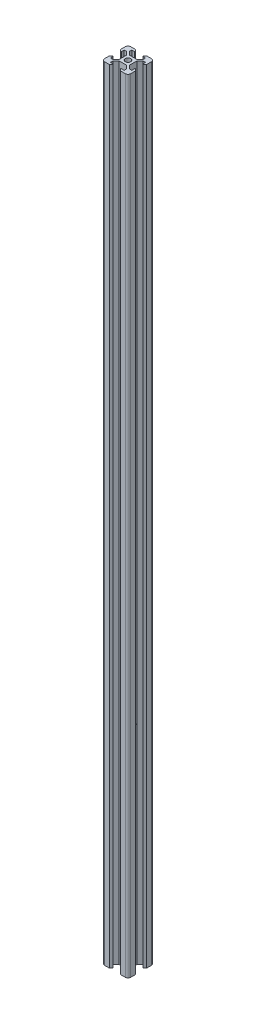
SolidWorks part; units mm, degrees
material "6063-T6"
ref_plane "Alzado" through (0, 0, 0) normal (0, 0, 1) x (1, 0, 0)
ref_plane "Planta" through (0, 0, 0) normal (0, 1, 0) x (1, 0, 0)
ref_plane "Vista lateral" through (0, 0, 0) normal (1, 0, 0) x (0, 0, -1)
sketch "Croquis1" plane through (0, 0, 0) normal (0, 1, 0) x (1, 0, 0)
  line L0 (0, 0) -> (-10, 10) construction
  line L1 (3.9, -2.84) -> (3.9, 2.84)
  line L2 (8.2, 5.3) -> (8.2, 3.34)
  line L3 (10, 8) -> (10, 4.14)
  line L4 (8.2, 5.3) -> (6.36, 5.3)
  line L5 (3.9, 2.84) -> (6.36, 5.3)
  line L6 (8.7, 2.84) -> (10, 4.14)
  line L7 (0, 0) -> (10, 10) construction
  line L8 (8, 10) -> (4.14, 10)
  line L9 (2.84, 8.7) -> (4.14, 10)
  line L10 (5.3, 8.2) -> (3.34, 8.2)
  line L11 (5.3, 8.2) -> (5.3, 6.36)
  line L12 (2.84, 3.9) -> (5.3, 6.36)
  line L13 (-2.84, 3.9) -> (2.84, 3.9)
  line L14 (-2.84, -3.9) -> (-5.3, -6.36)
  line L15 (-30.7915, 0) -> (30.7915, 0) construction
  line L16 (3.9, -2.84) -> (6.36, -5.3)
  line L17 (8.2, -5.3) -> (6.36, -5.3)
  line L18 (8.2, -5.3) -> (8.2, -3.34)
  line L19 (8.7, -2.84) -> (10, -4.14)
  line L20 (10, -8) -> (10, -4.14)
  line L21 (8, -10) -> (4.14, -10)
  line L22 (2.84, -8.7) -> (4.14, -10)
  line L23 (5.3, -8.2) -> (3.34, -8.2)
  line L24 (5.3, -8.2) -> (5.3, -6.36)
  line L25 (2.84, -3.9) -> (5.3, -6.36)
  line L26 (-2.84, -3.9) -> (2.84, -3.9)
  line L27 (0, 0) -> (0, 15.4885) construction
  line L28 (0, 0) -> (0, -17.6665) construction
  line L29 (0, 0) -> (-18.0561, 0) construction
  line L30 (-5.3, -8.2) -> (-5.3, -6.36)
  line L31 (-5.3, -8.2) -> (-3.34, -8.2)
  line L32 (-2.84, -8.7) -> (-4.14, -10)
  line L33 (-8, -10) -> (-4.14, -10)
  line L34 (-10, -8) -> (-10, -4.14)
  line L35 (-8.7, -2.84) -> (-10, -4.14)
  line L36 (-8.2, -5.3) -> (-8.2, -3.34)
  line L37 (-8.2, -5.3) -> (-6.36, -5.3)
  line L38 (-3.9, -2.84) -> (-6.36, -5.3)
  line L39 (-2.84, 3.9) -> (-5.3, 6.36)
  line L40 (-5.3, 8.2) -> (-5.3, 6.36)
  line L41 (-5.3, 8.2) -> (-3.34, 8.2)
  line L42 (-2.84, 8.7) -> (-4.14, 10)
  line L43 (-8, 10) -> (-4.14, 10)
  line L44 (-8.7, 2.84) -> (-10, 4.14)
  line L45 (-3.9, 2.84) -> (-6.36, 5.3)
  line L46 (-8.2, 5.3) -> (-6.36, 5.3)
  line L47 (-10, 8) -> (-10, 4.14)
  line L48 (-8.2, 5.3) -> (-8.2, 3.34)
  line L49 (-3.9, -2.84) -> (-3.9, 2.84)
  arc A0 (8.2, 3.34) -> (8.7, 2.84) centre (8.7, 3.34) ccw
  arc A1 (3.34, 8.2) -> (2.84, 8.7) centre (3.34, 8.7) cw
  arc A2 (10, 8) -> (8, 10) centre (8, 8) ccw
  arc A3 (8.2, -3.34) -> (8.7, -2.84) centre (8.7, -3.34) cw
  arc A4 (10, -8) -> (8, -10) centre (8, -8) cw
  arc A5 (3.34, -8.2) -> (2.84, -8.7) centre (3.34, -8.7) ccw
  arc A6 (-3.34, -8.2) -> (-2.84, -8.7) centre (-3.34, -8.7) cw
  arc A7 (-10, -8) -> (-8, -10) centre (-8, -8) ccw
  arc A8 (-8.2, -3.34) -> (-8.7, -2.84) centre (-8.7, -3.34) ccw
  arc A9 (-10, 8) -> (-8, 10) centre (-8, 8) cw
  arc A10 (-3.34, 8.2) -> (-2.84, 8.7) centre (-3.34, 8.7) ccw
  arc A11 (-8.2, 3.34) -> (-8.7, 2.84) centre (-8.7, 3.34) cw
  circle A12 centre (0, 0) radius 2.1
  point P11 (8.2, 2.84)
  point P65 (0, -3.9)
  point P73 (0, 3.9)
  point P80 (-8.2, 2.84)
  dimension "D9" = 0.5
  dimension "D12" = 2
  dimension "D13" = 4.2
  dimension "D2" = 3.9
  dimension "D3" = 3.9
  dimension "D4" = 2.46
  dimension "D5" = 5.86
  dimension "D6" = 1.96
  dimension "D7" = 0.7495
  dimension "D8" = 10
  dimension "D10" = 1.84
  dimension "D11" = 1.3
extrude "Saliente-Extruir2" add sketch "Croquis1" along normal blind 600
sketch "Croquis2" plane through (0, 0, 0) normal (1, 0, 0) x (0, 0, -1)
  line L0 (0, 0) -> (0, 160)
  circle A0 centre (0, 160) radius 2.1
  dimension "D2" = 4.2
  dimension "D1" = 160
extrude "Cortar-Extruir2" cut sketch "Croquis2" against normal mid plane 350 contours A0
